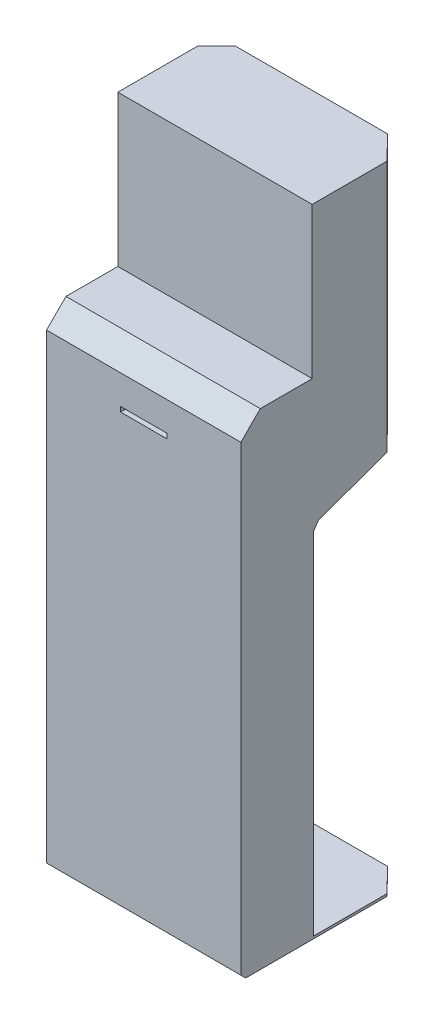
SolidWorks part; units mm, degrees
ref_plane "Front Plane" through (0, 0, 0) normal (0, 0, 1) x (1, 0, 0)
ref_plane "Top Plane" through (0, 0, 0) normal (0, 1, 0) x (1, 0, 0)
ref_plane "Right Plane" through (0, 0, 0) normal (1, 0, 0) x (0, 0, -1)
sketch "Sketch1" plane through (0, 0, 0) normal (1, 0, 0) x (0, 0, -1)
  line L0 (0, 0) -> (-340, 0)
  line L1 (-350, 10) -> (-350, 960)
  line L2 (-310, 1000) -> (-203.2511, 1000)
  line L3 (-203.2511, 1000) -> (-203.2511, 1310.6969)
  line L4 (0, 970) -> (0, 820)
  line L5 (-203.2511, 1310.6969) -> (-350, 1000) construction
  line L6 (-203.2511, 1310.6969) -> (-108.4889, 1310.6969)
  line L7 (-108.4889, 1310.6969) -> (-9.8898, 1028.323) construction
  line L8 (-310, 1000) -> (-350, 960)
  line L9 (-27.4748, 800) -> (-180, 800) construction
  line L10 (-200, 780) -> (-200, 20) construction
  line L11 (-190, 10) -> (0, 10) construction
  line L12 (0, 10) -> (0, 0) construction
  line L13 (-200, 20) -> (-190, 10) construction
  line L14 (-340, 0) -> (-350, 10)
  line L15 (-180, 800) -> (-200, 780) construction
  line L16 (-9.3969, 806.5798) -> (-27.4748, 800)
  line L17 (-27.4748, 800) -> (-190.6031, 740.6262)
  line L18 (-200, 727.206) -> (-200, 5)
  line L19 (0, 1000) -> (0, 1310.6969)
  line L20 (0, 1310.6969) -> (-108.4889, 1310.6969)
  line L21 (-9.8898, 1028.323) -> (0, 970) construction
  line L22 (0, 820) -> (-9.3969, 806.5798)
  line L23 (-190.6031, 740.6262) -> (-200, 727.206)
  line L24 (0, 1000) -> (0, 970)
  line L25 (0, 10) -> (-200, 70) construction
  line L26 (-200, 5) -> (0, 5)
  line L27 (0, 5) -> (0, 0)
  arc A0 (0, 1000) -> (-203.2511, 1310.6969) centre (-339.0968, 1000) ccw construction
  arc A1 (-350, 960) -> (-310, 1000) centre (-310, 960) cw construction
  point P1 (-350, 0)
  point P12 (0, 800)
  point P13 (-200, 800)
  point P15 (-200, 10)
  point P23 (0, 810)
  point P25 (-200, 737.206)
  dimension "D5" = 40
  dimension "D1" = 1000
  dimension "D2" = 350
  dimension "D3" = 310.6969
  dimension "D7" = 150
  dimension "D8" = 10
  dimension "D10" = 110
  dimension "D9" = 200
  dimension "D15" = 60
  dimension "D16" = 5
extrude "Boss-Extrude1" add sketch "Sketch1" along normal blind 400
sketch "Sketch3" plane through (0, 0, 0) normal (0, -1, 0) x (-1, 0, 0)
  line L0 (32.9719, -72.8044) -> (-67.7282, 29.5696)
  line L1 (-67.7282, 29.5696) -> (-322.6486, 29.5696)
  line L2 (-322.6486, 29.5696) -> (-423.3487, -72.8044)
  line L3 (-423.3487, -72.8044) -> (-423.3487, 100.0695)
  line L4 (-423.3487, 100.0695) -> (32.9719, 100.0695)
  line L5 (32.9719, 100.0695) -> (32.9719, -72.8044)
  line L6 (-195.1884, 29.5696) -> (-195.1884, -2.4875) construction
  line L8 (-195.1884, 29.5696) -> (-195.1884, 100.0695) construction
extrude "Cut-Extrude2" cut sketch "Sketch3" against normal through all both and the other way through all
sketch "Sketch4" plane through (0, 0, 350) normal (0, 0, 1) x (1, 0, 0)
  line L0 (152.5, 895) -> (0, 895) construction
  line L1 (152.5, 900) -> (247.5, 900)
  line L2 (152.5, 900) -> (152.5, 890)
  line L3 (152.5, 890) -> (247.5, 890)
  line L4 (247.5, 900) -> (247.5, 890)
  line L5 (0, 960) -> (0, 10) construction
  line L6 (200, 900) -> (200, 1000) construction
  line L7 (400, 1000) -> (0, 1000) construction
  dimension "D1" = 95
  dimension "D2" = 10
  dimension "D3" = 100
extrude "Cut-Extrude3" cut sketch "Sketch4" against normal blind 109
